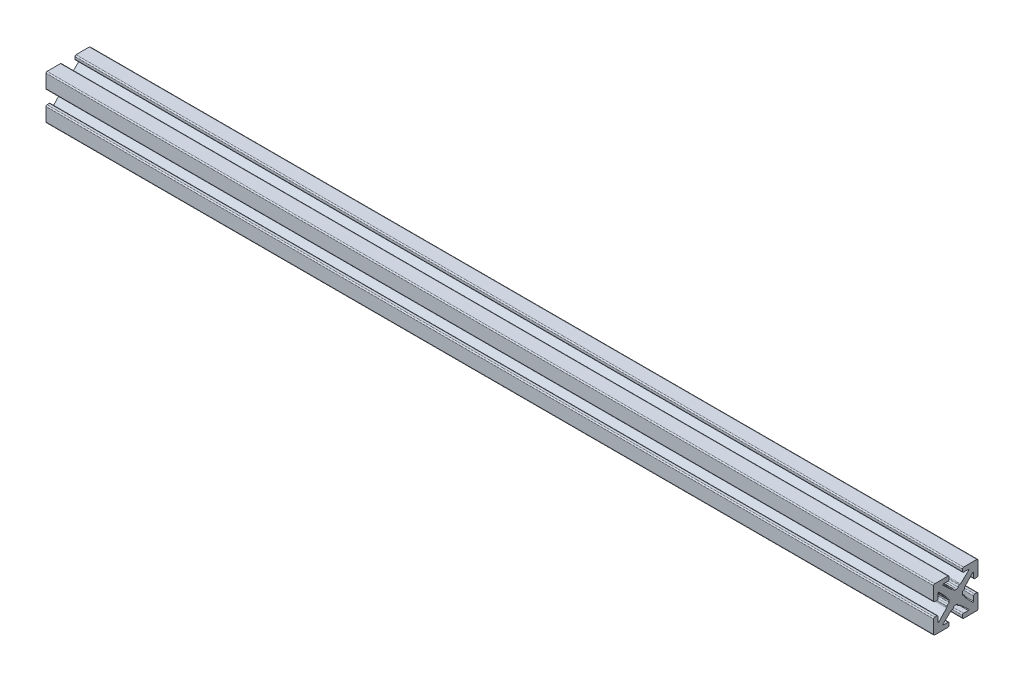
SolidWorks part; units mm, degrees
ref_plane "Front Plane" through (0, 0, 0) normal (0, 0, 1) x (1, 0, 0)
ref_plane "Top Plane" through (0, 0, 0) normal (0, 1, 0) x (1, 0, 0)
ref_plane "Right Plane" through (0, 0, 0) normal (1, 0, 0) x (0, 0, -1)
sketch "Sketch1" plane through (0, 0, 0) normal (1, 0, 0) x (0, 0, -1)
  line L0 (0, 0) -> (0, 1.4986) construction
  line L1 (-0.2413, 1.4986) -> (0.2413, 1.4986)
  line L2 (5.0038, 1.7526) -> (5.0038, 4.7498)
  line L3 (0.7493, 2.0066) -> (0.8899, 2.0066)
  line L4 (1.0639, 2.0756) -> (2.8908, 3.7937)
  line L5 (2.8038, 4.0132) -> (1.7526, 4.0132)
  line L6 (1.4986, 4.2672) -> (1.4986, 4.7498)
  line L7 (1.7526, 5.0038) -> (4.7498, 5.0038)
  line L8 (5.0038, 5.0038) -> (0, 0) construction
  line L9 (0, 0) -> (8.6271, 0) construction
  line L10 (0, 0) -> (0, 5.0038) construction
  line L11 (4.2672, 1.4986) -> (4.7498, 1.4986)
  line L12 (4.0132, 2.8038) -> (4.0132, 1.7526)
  line L13 (2.0756, 1.0639) -> (3.7937, 2.8908)
  line L14 (2.0066, 0.7493) -> (2.0066, 0.8899)
  line L15 (1.4986, -0.2413) -> (1.4986, 0.2413)
  line L16 (0, 0) -> (1.4986, 0) construction
  line L17 (-0.2413, -1.4986) -> (0.2413, -1.4986)
  line L18 (0.7493, -2.0066) -> (0.8899, -2.0066)
  line L19 (1.0639, -2.0756) -> (2.8908, -3.7937)
  line L20 (2.8038, -4.0132) -> (1.7526, -4.0132)
  line L21 (1.4986, -4.2672) -> (1.4986, -4.7498)
  line L22 (1.7526, -5.0038) -> (4.7498, -5.0038)
  line L23 (5.0038, -1.7526) -> (5.0038, -4.7498)
  line L24 (4.2672, -1.4986) -> (4.7498, -1.4986)
  line L25 (4.0132, -2.8038) -> (4.0132, -1.7526)
  line L26 (2.0756, -1.0639) -> (3.7937, -2.8908)
  line L27 (2.0066, -0.7493) -> (2.0066, -0.8899)
  line L28 (-0.7493, 2.0066) -> (-0.8899, 2.0066)
  line L29 (-1.0639, 2.0756) -> (-2.8908, 3.7937)
  line L30 (-2.8038, 4.0132) -> (-1.7526, 4.0132)
  line L31 (-1.4986, 4.2672) -> (-1.4986, 4.7498)
  line L32 (-1.7526, 5.0038) -> (-4.7498, 5.0038)
  line L33 (-5.0038, 1.7526) -> (-5.0038, 4.7498)
  line L34 (-4.2672, 1.4986) -> (-4.7498, 1.4986)
  line L35 (-4.0132, 2.8038) -> (-4.0132, 1.7526)
  line L36 (-2.0756, 1.0639) -> (-3.7937, 2.8908)
  line L37 (-2.0066, 0.7493) -> (-2.0066, 0.8899)
  line L38 (-1.4986, -0.2413) -> (-1.4986, 0.2413)
  line L39 (-2.0066, -0.7493) -> (-2.0066, -0.8899)
  line L40 (-2.0756, -1.0639) -> (-3.7937, -2.8908)
  line L41 (-4.0132, -2.8038) -> (-4.0132, -1.7526)
  line L42 (-4.2672, -1.4986) -> (-4.7498, -1.4986)
  line L43 (-5.0038, -1.7526) -> (-5.0038, -4.7498)
  line L44 (-1.7526, -5.0038) -> (-4.7498, -5.0038)
  line L45 (-1.4986, -4.2672) -> (-1.4986, -4.7498)
  line L46 (-2.8038, -4.0132) -> (-1.7526, -4.0132)
  line L47 (-1.0639, -2.0756) -> (-2.8908, -3.7937)
  line L48 (-0.7493, -2.0066) -> (-0.8899, -2.0066)
  arc A0 (2.8908, 3.7937) -> (2.8038, 4.0132) centre (2.8038, 3.8862) ccw
  arc A1 (0.4953, 1.7526) -> (0.7493, 2.0066) centre (0.7493, 1.7526) cw
  arc A2 (0.8899, 2.0066) -> (1.0639, 2.0756) centre (0.8899, 2.2606) ccw
  arc A3 (1.7526, 4.0132) -> (1.4986, 4.2672) centre (1.7526, 4.2672) cw
  arc A4 (1.4986, 4.7498) -> (1.7526, 5.0038) centre (1.7526, 4.7498) cw
  arc A5 (0.2413, 1.4986) -> (0.4953, 1.7526) centre (0.2413, 1.7526) ccw
  arc A6 (4.7498, 1.4986) -> (5.0038, 1.7526) centre (4.7498, 1.7526) ccw
  arc A7 (4.0132, 1.7526) -> (4.2672, 1.4986) centre (4.2672, 1.7526) ccw
  arc A8 (3.7937, 2.8908) -> (4.0132, 2.8038) centre (3.8862, 2.8038) cw
  arc A9 (2.0066, 0.8899) -> (2.0756, 1.0639) centre (2.2606, 0.8899) cw
  arc A10 (1.7526, 0.4953) -> (2.0066, 0.7493) centre (1.7526, 0.7493) ccw
  arc A11 (1.4986, 0.2413) -> (1.7526, 0.4953) centre (1.7526, 0.2413) cw
  arc A12 (0.2413, -1.4986) -> (0.4953, -1.7526) centre (0.2413, -1.7526) cw
  arc A13 (0.4953, -1.7526) -> (0.7493, -2.0066) centre (0.7493, -1.7526) ccw
  arc A14 (0.8899, -2.0066) -> (1.0639, -2.0756) centre (0.8899, -2.2606) cw
  arc A15 (2.8908, -3.7937) -> (2.8038, -4.0132) centre (2.8038, -3.8862) cw
  arc A16 (1.7526, -4.0132) -> (1.4986, -4.2672) centre (1.7526, -4.2672) ccw
  arc A17 (1.4986, -4.7498) -> (1.7526, -5.0038) centre (1.7526, -4.7498) ccw
  arc A18 (4.7498, -1.4986) -> (5.0038, -1.7526) centre (4.7498, -1.7526) cw
  arc A19 (4.0132, -1.7526) -> (4.2672, -1.4986) centre (4.2672, -1.7526) cw
  arc A20 (3.7937, -2.8908) -> (4.0132, -2.8038) centre (3.8862, -2.8038) ccw
  arc A21 (2.0066, -0.8899) -> (2.0756, -1.0639) centre (2.2606, -0.8899) ccw
  arc A22 (1.7526, -0.4953) -> (2.0066, -0.7493) centre (1.7526, -0.7493) cw
  arc A23 (1.4986, -0.2413) -> (1.7526, -0.4953) centre (1.7526, -0.2413) ccw
  arc A24 (-0.2413, 1.4986) -> (-0.4953, 1.7526) centre (-0.2413, 1.7526) cw
  arc A25 (-0.4953, 1.7526) -> (-0.7493, 2.0066) centre (-0.7493, 1.7526) ccw
  arc A26 (-0.8899, 2.0066) -> (-1.0639, 2.0756) centre (-0.8899, 2.2606) cw
  arc A27 (-2.8908, 3.7937) -> (-2.8038, 4.0132) centre (-2.8038, 3.8862) cw
  arc A28 (-1.7526, 4.0132) -> (-1.4986, 4.2672) centre (-1.7526, 4.2672) ccw
  arc A29 (-1.4986, 4.7498) -> (-1.7526, 5.0038) centre (-1.7526, 4.7498) ccw
  arc A30 (-4.7498, 1.4986) -> (-5.0038, 1.7526) centre (-4.7498, 1.7526) cw
  arc A31 (-4.0132, 1.7526) -> (-4.2672, 1.4986) centre (-4.2672, 1.7526) cw
  arc A32 (-3.7937, 2.8908) -> (-4.0132, 2.8038) centre (-3.8862, 2.8038) ccw
  arc A33 (-2.0066, 0.8899) -> (-2.0756, 1.0639) centre (-2.2606, 0.8899) ccw
  arc A34 (-1.7526, 0.4953) -> (-2.0066, 0.7493) centre (-1.7526, 0.7493) cw
  arc A35 (-1.4986, 0.2413) -> (-1.7526, 0.4953) centre (-1.7526, 0.2413) ccw
  arc A36 (-1.4986, -0.2413) -> (-1.7526, -0.4953) centre (-1.7526, -0.2413) cw
  arc A37 (-1.7526, -0.4953) -> (-2.0066, -0.7493) centre (-1.7526, -0.7493) ccw
  arc A38 (-2.0066, -0.8899) -> (-2.0756, -1.0639) centre (-2.2606, -0.8899) cw
  arc A39 (-3.7937, -2.8908) -> (-4.0132, -2.8038) centre (-3.8862, -2.8038) cw
  arc A40 (-4.0132, -1.7526) -> (-4.2672, -1.4986) centre (-4.2672, -1.7526) ccw
  arc A41 (-4.7498, -1.4986) -> (-5.0038, -1.7526) centre (-4.7498, -1.7526) ccw
  arc A42 (-1.4986, -4.7498) -> (-1.7526, -5.0038) centre (-1.7526, -4.7498) cw
  arc A43 (-1.7526, -4.0132) -> (-1.4986, -4.2672) centre (-1.7526, -4.2672) cw
  arc A44 (-2.8908, -3.7937) -> (-2.8038, -4.0132) centre (-2.8038, -3.8862) ccw
  arc A45 (-0.8899, -2.0066) -> (-1.0639, -2.0756) centre (-0.8899, -2.2606) ccw
  arc A46 (-0.4953, -1.7526) -> (-0.7493, -2.0066) centre (-0.7493, -1.7526) cw
  arc A47 (-0.2413, -1.4986) -> (-0.4953, -1.7526) centre (-0.2413, -1.7526) ccw
  arc A48 (-4.7498, 5.0038) -> (-5.0038, 4.7498) centre (-4.7498, 4.7498) ccw
  arc A49 (-5.0038, -4.7498) -> (-4.7498, -5.0038) centre (-4.7498, -4.7498) ccw
  arc A50 (4.7498, -5.0038) -> (5.0038, -4.7498) centre (4.7498, -4.7498) ccw
  arc A51 (4.7498, 5.0038) -> (5.0038, 4.7498) centre (4.7498, 4.7498) cw
  point P14 (3.1242, 4.0132)
  point P19 (0.9906, 2.0066)
  point P150 (0, -1.4986)
  point P152 (-5.0038, 5.0038)
  point P155 (-5.0038, -5.0038)
  point P158 (5.0038, -5.0038)
  dimension "D10" = 0.127
  dimension "D11" = 0.254
  dimension "D2" = 0.254
  dimension "D1" = 10.0076
  dimension "D3" = 2.9972
  dimension "D4" = 0.508
  dimension "D5" = 2.9972
  dimension "D6" = 0.9906
  dimension "D7" = 1.6256
  dimension "D8" = 1.9812
  dimension "D9" = 0.9906
extrude "Boss.-Extru.1" add sketch "Sketch1" along normal blind 200
